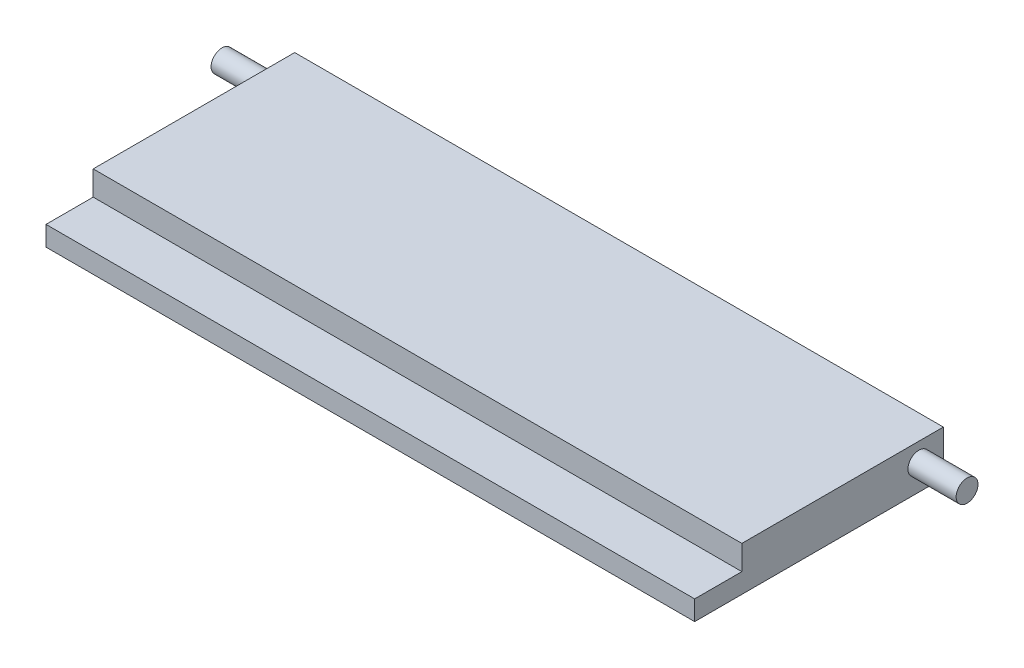
SolidWorks part; units mm, degrees
ref_plane "Front Plane" through (0, 0, 0) normal (0, 0, 1) x (1, 0, 0)
ref_plane "Top Plane" through (0, 0, 0) normal (0, 1, 0) x (1, 0, 0)
ref_plane "Right Plane" through (0, 0, 0) normal (1, 0, 0) x (0, 0, -1)
other "Configuration Table"
sketch "Sketch1" plane through (0, 0, 0) normal (0, 0, 1) x (1, 0, 0)
  line L1 (-32.9946, -2.2479) -> (32.9946, -2.2479)
  line L2 (-32.9946, -2.2479) -> (-32.9946, 2.2479)
  line L3 (-32.9946, 2.2479) -> (32.9946, 2.2479)
  line L4 (32.9946, -2.2479) -> (32.9946, 2.2479)
  line L5 (-32.9946, -2.2479) -> (32.9946, 2.2479) construction
  line L6 (-32.9946, 2.2479) -> (32.9946, -2.2479) construction
  point P0 (0, 0)
  dimension "D1" = 65.9892
  dimension "D2" = 4.4958
extrude "Boss-Extrude1" add sketch "Sketch1" along normal blind 20.4978
sketch "Sketch4" plane through (0, 0, 20.4978) normal (0, 0, 1) x (1, 0, 0)
  line L0 (-32.9946, 2.2479) -> (-32.9946, -2.2479) construction
  line L1 (-32.9946, -0.2413) -> (32.9946, -0.2413)
  line L2 (-32.9946, -0.2413) -> (-32.9946, -2.2479)
  line L3 (-32.9946, -2.2479) -> (32.9946, -2.2479)
  line L4 (32.9946, -0.2413) -> (32.9946, -2.2479)
  dimension "D1" = 2.0066
extrude "Boss-Extrude2" add sketch "Sketch4" along normal blind 4.8006
sketch "Sketch5" plane through (0, 0, 0) normal (1, 0, 0) x (0, 0, -1)
  line L0 (0, -2.2479) -> (0, 2.2479) construction
  line L1 (-25.2984, -2.2479) -> (0, -2.2479) construction
  circle A0 centre (-2.4892, 0.3429) radius 1.1125
  dimension "D1" = 2.225
  dimension "D2" = 2.4892
  dimension "D3" = 2.5908
extrude "Boss-Extrude3" add sketch "Sketch5" along normal mid plane 75.7936
